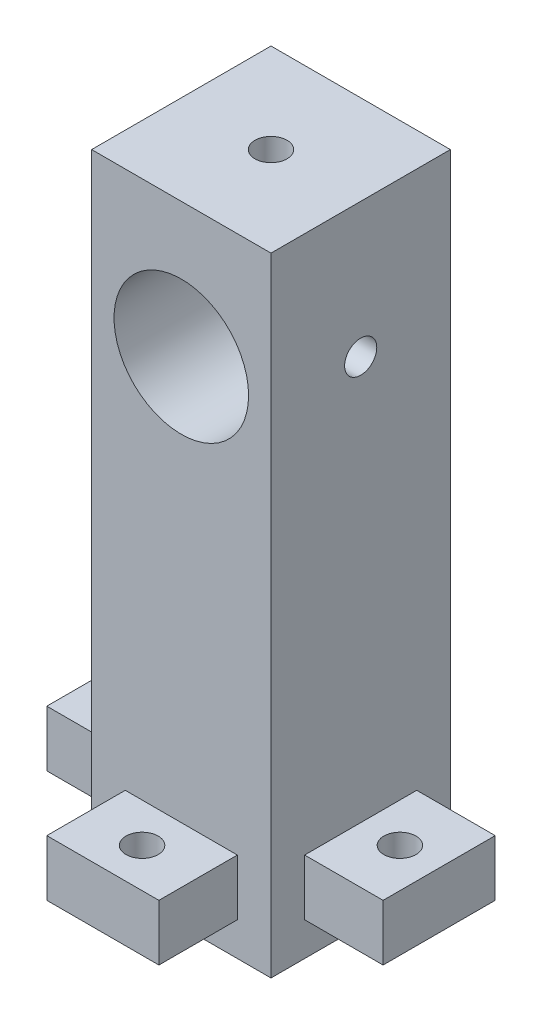
SolidWorks part; units mm, degrees
ref_plane "Alzado" through (0, 0, 0) normal (0, 0, 1) x (1, 0, 0)
ref_plane "Planta" through (0, 0, 0) normal (0, 1, 0) x (1, 0, 0)
ref_plane "Vista lateral" through (0, 0, 0) normal (1, 0, 0) x (0, 0, -1)
sketch "Croquis1" plane through (0, 0, 0) normal (0, 1, 0) x (1, 0, 0)
  line L1 (-8, 8) -> (8, 8)
  line L2 (-8, 8) -> (-8, -8)
  line L3 (-8, -8) -> (8, -8)
  line L4 (8, 8) -> (8, -8)
  line L5 (-8, 8) -> (8, -8) construction
  line L6 (-8, -8) -> (8, 8) construction
  point P0 (0, 0)
  dimension "D1" = 16
  dimension "D2" = 16
extrude "Saliente-Extruir1" add sketch "Croquis1" along normal blind 56
sketch "Croquis2" plane through (0, 0, 8) normal (0, 0, 1) x (1, 0, 0)
  line L0 (-8, 56) -> (8, 56) construction
  line L1 (8, 56) -> (8, 0) construction
  circle A0 centre (0, 44) radius 6
  dimension "D1" = 12
  dimension "D2" = 12
  dimension "D3" = 8
extrude "Cortar-Extruir1" cut sketch "Croquis2" against normal up to next
sketch "Croquis3" plane through (8, 0, 0) normal (1, 0, 0) x (0, 0, -1)
  line L0 (8, 56) -> (8, 0) construction
  line L2 (-8, 56) -> (8, 56) construction
  circle A0 centre (0, 44) radius 1.435
  point P4 (0, 0)
  point P6 (-2.3874, 56)
  point P7 (0, 0)
  dimension "D3" = 2.87
  dimension "D1" = 8
  dimension "D2" = 12
extrude "Cortar-Extruir2" cut sketch "Croquis3" against normal blind 16
sketch "Croquis4" plane through (0, 56, 0) normal (0, 1, 0) x (1, 0, 0)
  circle A0 centre (0, 0) radius 1.435
  dimension "D1" = 2.87
extrude "Cortar-Extruir3" cut sketch "Croquis4" against normal up to next
sketch "Croquis5" plane through (-8, 0, 0) normal (-1, 0, 0) x (0, 0, 1)
  line L1 (5, 3) -> (-5, 3)
  line L2 (5, 3) -> (5, 8)
  line L3 (5, 8) -> (-5, 8)
  line L4 (-5, 3) -> (-5, 8)
  line L5 (8, 56) -> (8, 0) construction
  line L6 (-8, 0) -> (8, 0) construction
  dimension "D1" = 5
  dimension "D2" = 10
  dimension "D3" = 3
  dimension "D4" = 8
extrude "Saliente-Extruir2" add sketch "Croquis5" along normal blind 7
sketch "Croquis6" plane through (0, 8, 0) normal (0, 1, 0) x (1, 0, 0)
  line L0 (-8, -5) -> (-8, 5) construction
  line L1 (-15, -5) -> (-8, -5) construction
  circle A0 centre (-11.5, 0) radius 1.435
  dimension "D1" = 2.87
  dimension "D2" = 3.5
  dimension "D3" = 5
extrude "Cortar-Extruir4" cut sketch "Croquis6" against normal up to next (5 mm away) contours A0
mirror "Simetría1" about plane through (0, 0, 0) normal (1, 0, 0) of "Saliente-Extruir2", "Cortar-Extruir4"
sketch "Croquis7" plane through (0, 0, 8) normal (0, 0, 1) x (1, 0, 0)
  line L0 (-8, 3) -> (-8, 8) construction
  line L1 (5, 3) -> (-5, 3)
  line L2 (5, 3) -> (5, 8)
  line L3 (5, 8) -> (-5, 8)
  line L4 (-5, 3) -> (-5, 8)
  line L5 (-8, 0) -> (8, 0) construction
  dimension "D1" = 10
  dimension "D2" = 3
  dimension "D3" = 3
  dimension "D4" = 5
extrude "Saliente-Extruir3" add sketch "Croquis7" along normal blind 7
sketch "Croquis8" plane through (0, 8, 0) normal (0, 1, 0) x (1, 0, 0)
  line L0 (5, -8) -> (-5, -8) construction
  line L1 (5, -15) -> (5, -8) construction
  circle A0 centre (0, -11.5) radius 1.435
  dimension "D3" = 2.87
  dimension "D1" = 3.5
  dimension "D2" = 5
extrude "Cortar-Extruir5" cut sketch "Croquis8" against normal up to next
